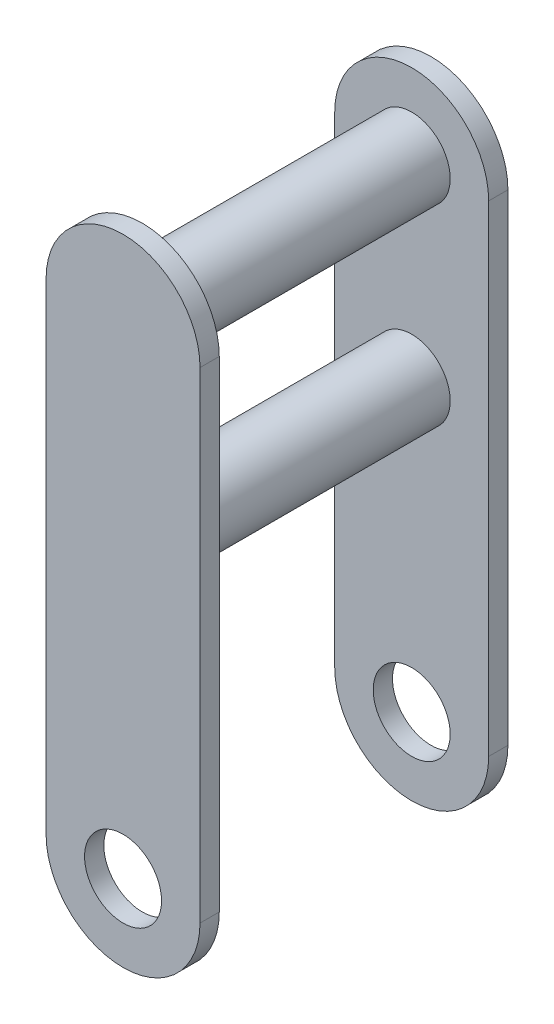
SolidWorks part; units mm, degrees
material "AISI 4340 Steel, normalized"
ref_plane "Front Plane" through (0, 0, 0) normal (0, 0, 1) x (1, 0, 0)
ref_plane "Top Plane" through (0, 0, 0) normal (0, 1, 0) x (1, 0, 0)
ref_plane "Right Plane" through (0, 0, 0) normal (1, 0, 0) x (0, 0, -1)
sketch "Sketch1" plane through (0, 0, 0) normal (0, 0, 1) x (1, 0, 0)
  line L0 (0, 0) -> (0, 250) construction
  line L1 (-40, 0) -> (-40, 250)
  line L2 (40, 0) -> (40, 250)
  arc A1 (-40, 0) -> (40, 0) centre (0, 0) ccw
  arc A2 (40, 250) -> (-40, 250) centre (0, 250) ccw
  circle A3 centre (0, 0) radius 20
  circle A4 centre (0, 250) radius 20 construction
  circle A5 centre (0, 150) radius 20 construction
  point P3 (0, 125)
  dimension "D2" = 40
  dimension "D3" = 20
  dimension "D1" = 250
  dimension "D4" = 100
extrude "Boss-Extrude1" add sketch "Sketch1" along normal mid plane 10 from offset 75
sketch "Sketch2" plane through (0, 0, 70) normal (0, 0, -1) x (-1, 0, 0)
  circle A0 centre (0, 250) radius 20 construction
  circle A1 centre (0, 150) radius 20 construction
  circle A2 centre (0, 250) radius 20
  circle A3 centre (0, 150) radius 20
extrude "Boss-Extrude2" add sketch "Sketch2" along normal blind 140
mirror "Mirror2" about plane through (0, 0, 0) normal (0, 0, 1) of "Boss-Extrude1"
